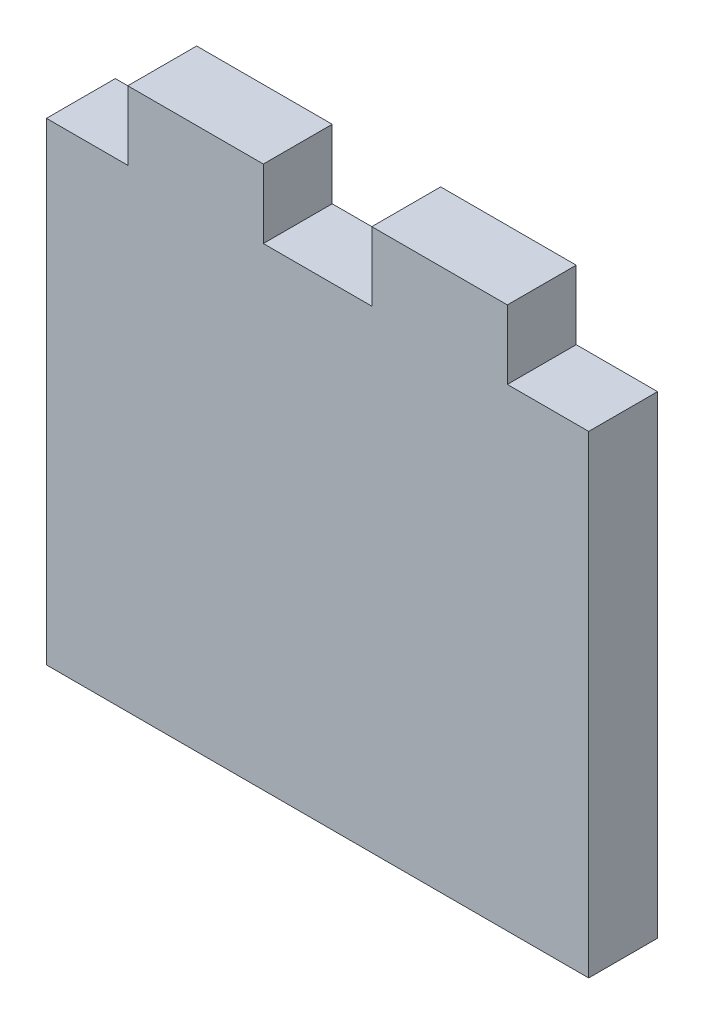
SolidWorks part; units mm, degrees
ref_plane "Front Plane" through (0, 0, 0) normal (0, 0, 1) x (1, 0, 0)
ref_plane "Top Plane" through (0, 0, 0) normal (0, 1, 0) x (1, 0, 0)
ref_plane "Right Plane" through (0, 0, 0) normal (1, 0, 0) x (0, 0, -1)
sketch "Sketch1" plane through (0, 0, 0) normal (0, 0, 1) x (1, 0, 0)
  line L1 (0, 0) -> (50, 0)
  line L2 (0, 0) -> (0, 50)
  line L3 (0, 50) -> (50, 50)
  line L4 (50, 0) -> (50, 50)
  dimension "D1" = 50
  dimension "D2" = 50
extrude "Boss-Extrude1" add sketch "Sketch1" along normal blind 6.35
sketch "Sketch2" plane through (0, 0, 6.35) normal (0, 0, 1) x (1, 0, 0)
  line L0 (50, 50) -> (0, 50) construction
  line L1 (50, 50) -> (42.5, 50)
  line L2 (50, 50) -> (50, 43.65)
  line L3 (50, 43.65) -> (42.5, 43.65)
  line L4 (42.5, 50) -> (42.5, 43.65)
  line L5 (0, 50) -> (7.5, 50)
  line L6 (0, 50) -> (0, 43.65)
  line L7 (0, 43.65) -> (7.5, 43.65)
  line L8 (7.5, 50) -> (7.5, 43.65)
  line L9 (20, 50) -> (30, 50)
  line L10 (20, 50) -> (20, 43.65)
  line L11 (20, 43.65) -> (30, 43.65)
  line L12 (30, 50) -> (30, 43.65)
  line L13 (7.5, 50) -> (20, 50) construction
  dimension "D1" = 6.35
  dimension "D2" = 7.5
  dimension "D3" = 6.35
  dimension "D4" = 7.5
  dimension "D5" = 10
  dimension "D6" = 6.35
  dimension "D7" = 12.5
extrude "Cut-Extrude1" cut sketch "Sketch2" against normal blind 6.35
